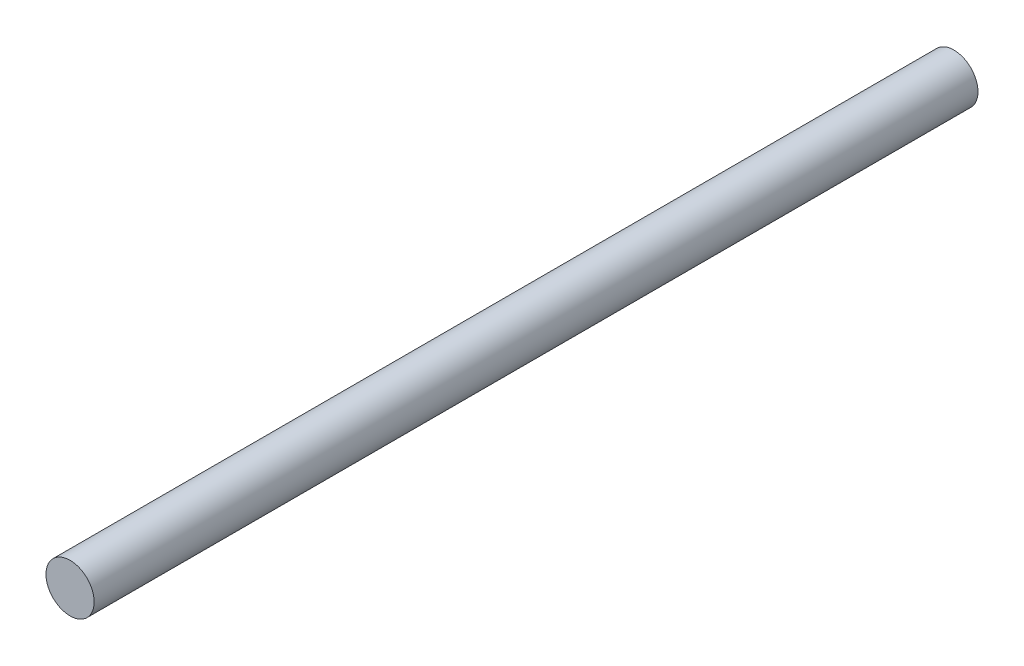
SolidWorks part; units mm, degrees
ref_plane "正面" through (0, 0, 0) normal (0, 0, 1) x (1, 0, 0)
ref_plane "平面" through (0, 0, 0) normal (0, 1, 0) x (1, 0, 0)
ref_plane "右側面" through (0, 0, 0) normal (1, 0, 0) x (0, 0, -1)
sketch "ｽｹｯﾁ1" plane through (0, 0, 0) normal (0, 0, 1) x (1, 0, 0)
  circle A0 centre (0, 0) radius 3
  dimension "D1" = 6
extrude "ﾎﾞｽ - 押し出し1" add sketch "ｽｹｯﾁ1" along normal blind 110
